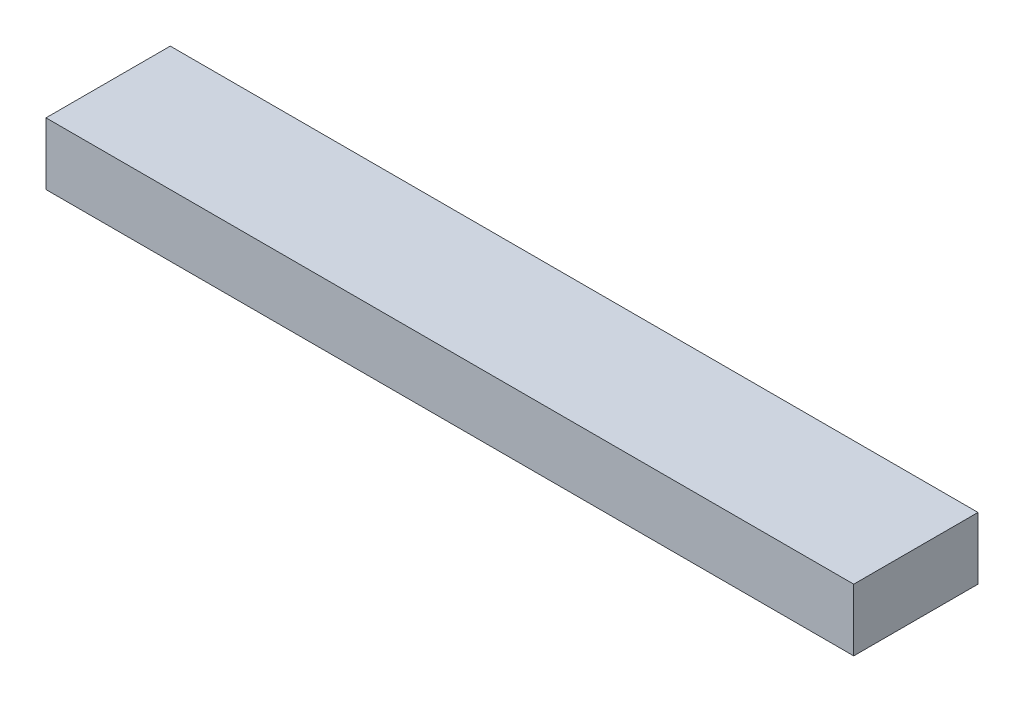
SolidWorks part; units mm, degrees
ref_plane "Front Plane" through (0, 0, 0) normal (0, 0, 1) x (1, 0, 0)
ref_plane "Top Plane" through (0, 0, 0) normal (0, 1, 0) x (1, 0, 0)
ref_plane "Right Plane" through (0, 0, 0) normal (1, 0, 0) x (0, 0, -1)
sketch "Sketch1" plane through (0, 0, 0) normal (0, 1, 0) x (1, 0, 0)
  line L1 (-32.5, -5) -> (32.5, -5)
  line L2 (-32.5, -5) -> (-32.5, 5)
  line L3 (-32.5, 5) -> (32.5, 5)
  line L4 (32.5, -5) -> (32.5, 5)
  line L5 (-32.5, -5) -> (32.5, 5) construction
  line L6 (-32.5, 5) -> (32.5, -5) construction
  point P0 (0, 0)
  dimension "D1" = 65
  dimension "D2" = 10
extrude "Boss-Extrude1" add sketch "Sketch1" along normal blind 5
